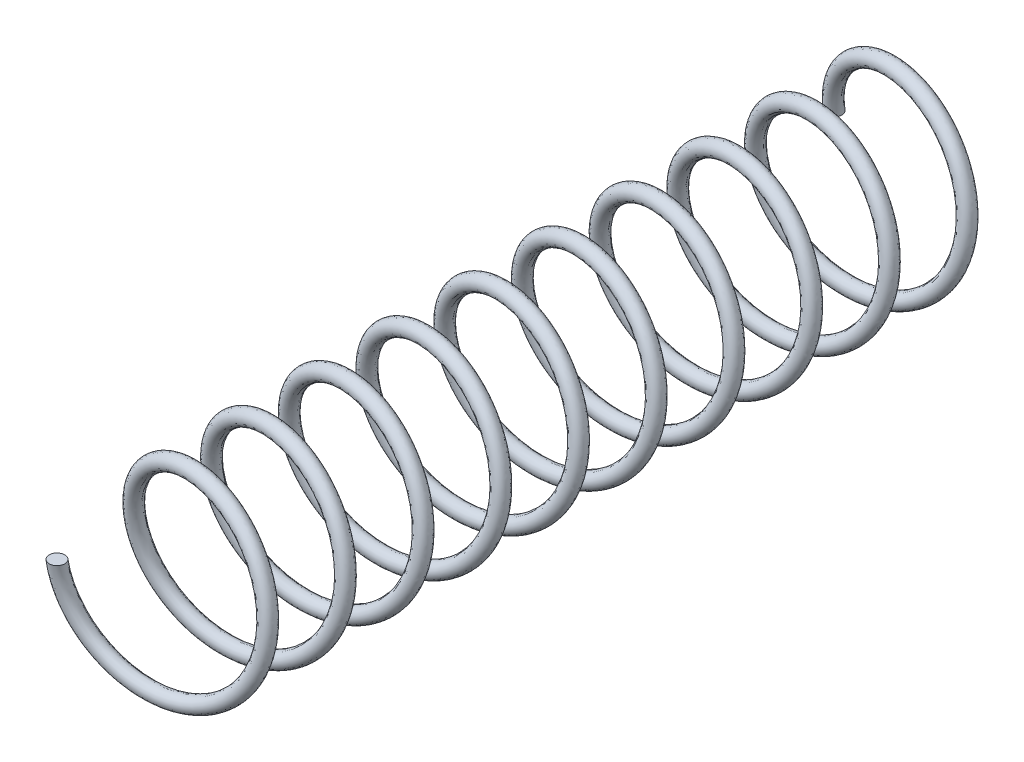
SolidWorks part; units mm, degrees
ref_plane "Front Plane" through (0, 0, 0) normal (0, 0, 1) x (1, 0, 0)
ref_plane "Top Plane" through (0, 0, 0) normal (0, 1, 0) x (1, 0, 0)
ref_plane "Right Plane" through (0, 0, 0) normal (1, 0, 0) x (0, 0, -1)
sketch "Sketch1" plane through (0, 0, 0) normal (0, 0, 1) x (1, 0, 0)
  circle A0 centre (0, 0) radius 5.5
  dimension "D1" = 11
curve "Helix/Spiral2" pitch 5 height 50 turns 10
sketch "Sketch2" plane through (0, 0, 0) normal (0, 1, 0) x (1, 0, 0)
  circle A0 centre (-5.5, -50) radius 0.5
  spline S0 degree 3 poles (-5.5, 0) (-5.5, -0.1035) (-5.2136, -0.3128) (-3.9903, -0.6249) (-2.1596, -0.9375) (0, -1.25) (2.1596, -1.5625) (3.9903, -1.875) (5.2136, -2.1875) (5.6432, -2.5) (5.2136, -2.8125) (3.9903, -3.125) (2.1596, -3.4375) (0, -3.75) (-2.1596, -4.0625) (-3.9903, -4.375) (-5.2136, -4.6875) (-5.6432, -5) (-5.2136, -5.3125) (-3.9903, -5.625) (-2.1596, -5.9375) (0, -6.25) (2.1596, -6.5625) (3.9903, -6.875) (5.2136, -7.1875) (5.6432, -7.5) (5.2136, -7.8125) (3.9903, -8.125) (2.1596, -8.4375) (0, -8.75) (-2.1596, -9.0625) (-3.9903, -9.375) (-5.2136, -9.6875) (-5.6432, -10) (-5.2136, -10.3125) (-3.9903, -10.625) (-2.1596, -10.9375) (0, -11.25) (2.1596, -11.5625) (3.9903, -11.875) (5.2136, -12.1875) (5.6432, -12.5) (5.2136, -12.8125) (3.9903, -13.125) (2.1596, -13.4375) (0, -13.75) (-2.1596, -14.0625) (-3.9903, -14.375) (-5.2136, -14.6875) (-5.6432, -15) (-5.2136, -15.3125) (-3.9903, -15.625) (-2.1596, -15.9375) (0, -16.25) (2.1596, -16.5625) (3.9903, -16.875) (5.2136, -17.1875) (5.6432, -17.5) (5.2136, -17.8125) (3.9903, -18.125) (2.1596, -18.4375) (0, -18.75) (-2.1596, -19.0625) (-3.9903, -19.375) (-5.2136, -19.6875) (-5.6432, -20) (-5.2136, -20.3125) (-3.9903, -20.625) (-2.1596, -20.9375) (0, -21.25) (2.1596, -21.5625) (3.9903, -21.875) (5.2136, -22.1875) (5.6432, -22.5) (5.2136, -22.8125) (3.9903, -23.125) (2.1596, -23.4375) (0, -23.75) (-2.1596, -24.0625) (-3.9903, -24.375) (-5.2136, -24.6875) (-5.6432, -25) (-5.2136, -25.3125) (-3.9903, -25.625) (-2.1596, -25.9375) (0, -26.25) (2.1596, -26.5625) (3.9903, -26.875) (5.2136, -27.1875) (5.6432, -27.5) (5.2136, -27.8125) (3.9903, -28.125) (2.1596, -28.4375) (0, -28.75) (-2.1596, -29.0625) (-3.9903, -29.375) (-5.2136, -29.6875) (-5.6432, -30) (-5.2136, -30.3125) (-3.9903, -30.625) (-2.1596, -30.9375) (0, -31.25) (2.1596, -31.5625) (3.9903, -31.875) (5.2136, -32.1875) (5.6432, -32.5) (5.2136, -32.8125) (3.9903, -33.125) (2.1596, -33.4375) (0, -33.75) (-2.1596, -34.0625) (-3.9903, -34.375) (-5.2136, -34.6875) (-5.6432, -35) (-5.2136, -35.3125) (-3.9903, -35.625) (-2.1596, -35.9375) (0, -36.25) (2.1596, -36.5625) (3.9903, -36.875) (5.2136, -37.1875) (5.6432, -37.5) (5.2136, -37.8125) (3.9903, -38.125) (2.1596, -38.4375) (0, -38.75) (-2.1596, -39.0625) (-3.9903, -39.375) (-5.2136, -39.6875) (-5.6432, -40) (-5.2136, -40.3125) (-3.9903, -40.625) (-2.1596, -40.9375) (0, -41.25) (2.1596, -41.5625) (3.9903, -41.875) (5.2136, -42.1875) (5.6432, -42.5) (5.2136, -42.8125) (3.9903, -43.125) (2.1596, -43.4375) (0, -43.75) (-2.1596, -44.0625) (-3.9903, -44.375) (-5.2136, -44.6875) (-5.6432, -45) (-5.2136, -45.3125) (-3.9903, -45.625) (-2.1596, -45.9375) (0, -46.25) (2.1596, -46.5625) (3.9903, -46.875) (5.2136, -47.1875) (5.6432, -47.5) (5.2136, -47.8125) (3.9903, -48.125) (2.1596, -48.4375) (0, -48.75) (-2.1596, -49.0625) (-3.9903, -49.3751) (-5.2136, -49.6872) (-5.5, -49.8965) (-5.5, -50) knots 0 0 0 0 0.00625 0.0125 0.01875 0.025 0.03125 0.0375 0.04375 0.05 0.05625 0.0625 0.06875 0.075 0.08125 0.0875 0.09375 0.1 0.10625 0.1125 0.11875 0.125 0.13125 0.1375 0.14375 0.15 0.15625 0.1625 0.16875 0.175 0.18125 0.1875 0.19375 0.2 0.20625 0.2125 0.21875 0.225 0.23125 0.2375 0.24375 0.25 0.25625 0.2625 0.26875 0.275 0.28125 0.2875 0.29375 0.3 0.30625 0.3125 0.31875 0.325 0.33125 0.3375 0.34375 0.35 0.35625 0.3625 0.36875 0.375 0.38125 0.3875 0.39375 0.4 0.40625 0.4125 0.41875 0.425 0.43125 0.4375 0.44375 0.45 0.45625 0.4625 0.46875 0.475 0.48125 0.4875 0.49375 0.5 0.50625 0.5125 0.51875 0.525 0.53125 0.5375 0.54375 0.55 0.55625 0.5625 0.56875 0.575 0.58125 0.5875 0.59375 0.6 0.60625 0.6125 0.61875 0.625 0.63125 0.6375 0.64375 0.65 0.65625 0.6625 0.66875 0.675 0.68125 0.6875 0.69375 0.7 0.70625 0.7125 0.71875 0.725 0.73125 0.7375 0.74375 0.75 0.75625 0.7625 0.76875 0.775 0.78125 0.7875 0.79375 0.8 0.80625 0.8125 0.81875 0.825 0.83125 0.8375 0.84375 0.85 0.85625 0.8625 0.86875 0.875 0.88125 0.8875 0.89375 0.9 0.90625 0.9125 0.91875 0.925 0.93125 0.9375 0.94375 0.95 0.95625 0.9625 0.96875 0.975 0.98125 0.9875 0.99375 1 1 1 1 construction
sweep "Sweep1" add profiles "Sketch2" path "Helix/Spiral2"
